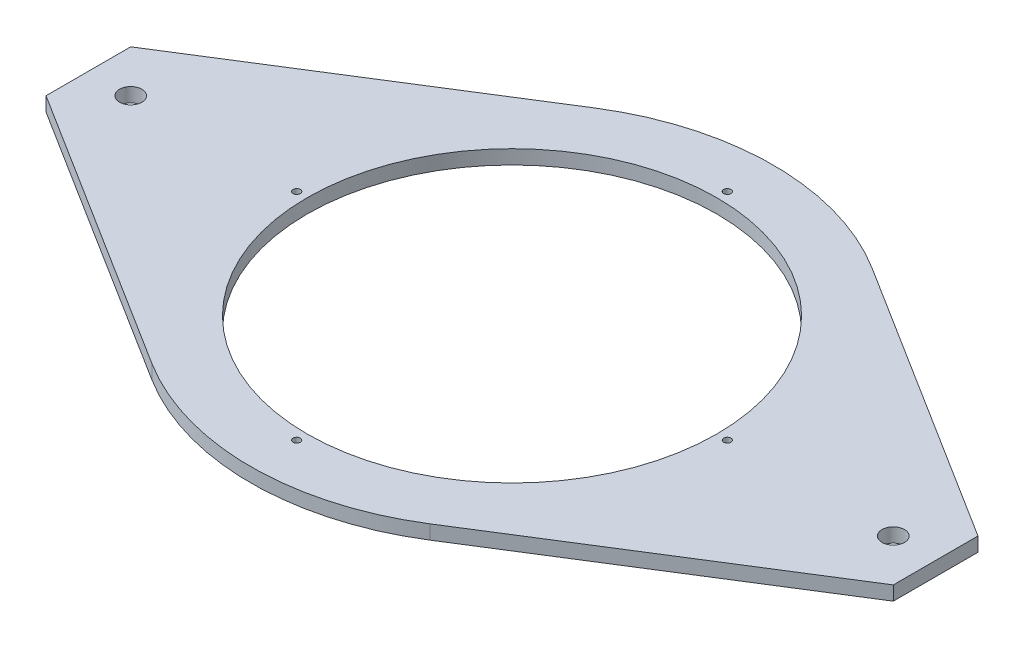
SolidWorks part; units mm, degrees
material "6061-T6 (SS)"
ref_plane "Front Plane" through (0, 0, 0) normal (0, 0, 1) x (1, 0, 0)
ref_plane "Top Plane" through (0, 0, 0) normal (0, 1, 0) x (1, 0, 0)
ref_plane "Right Plane" through (0, 0, 0) normal (1, 0, 0) x (0, 0, -1)
sketch "Sketch1" plane through (0, 0, 0) normal (0, 1, 0) x (1, 0, 0)
  line L2 (-190.5, 19.05) -> (-190.5, -19.05)
  line L4 (190.5, 19.05) -> (190.5, -19.05)
  line L5 (-190.5, 19.05) -> (190.5, -19.05) construction
  line L6 (-190.5, -19.05) -> (190.5, 19.05) construction
  line L8 (-190.5, 19.05) -> (-62.4957, 99.4719)
  line L9 (-190.5, -19.05) -> (-62.4957, -99.4719)
  line L10 (190.5, 19.05) -> (62.4957, 99.4719)
  line L11 (190.5, -19.05) -> (62.4957, -99.4719)
  circle A0 centre (0, 0) radius 92.075
  arc A1 (-62.4957, -99.4719) -> (62.4957, -99.4719) centre (0, 0) ccw
  arc A2 (62.4957, 99.4719) -> (-62.4957, 99.4719) centre (0, 0) ccw
  point P0 (0, 0)
  dimension "D3" = 184.15
  dimension "D4" = 25.4
  dimension "D1" = 381
  dimension "D2" = 38.1
extrude "Boss-Extrude1" add sketch "Sketch1" along normal blind 6.35
hole_wizard "#4 Clearance Hole1" positions "Sketch2" profile "Sketch3" hole size "#4" standard "ANSI Inch" end condition through all
sketch "Sketch2" plane through (0, 6.35, 0) normal (0, 1, 0) x (1, 0, 0)
  circle A0 centre (0, 0) radius 96.8375
  circle A1 centre (0, 0) radius 92.075 construction
  point P7 (0, 96.8375)
  point P9 (96.8375, 0)
  point P11 (0, -96.8375)
  point P13 (-96.8375, 0)
  dimension "D1" = 4.7625
sketch "Sketch3" plane through (0, 6.35, -96.8375) normal (1, 0, 0) x (0, 0, 1)
  line L0 (0, 0) -> (0, 6.35)
  line L1 (0, 6.35) -> (1.6319, 6.35)
  line L2 (1.6319, 6.35) -> (1.6319, 0)
  line L5 (1.6319, 0) -> (0, 0)
  line L11 (0, -6.35) -> (0, 107.95) construction
  dimension "Thru Hole Dia." = 3.2639
  dimension "Thru Hole Depth" = 6.35
hole_wizard "3/8 Clearance Hole1" positions "Sketch4" profile "Sketch5" hole size "3/8" standard "ANSI Inch" end condition through all
sketch "Sketch4" plane through (0, 6.35, 0) normal (0, 1, 0) x (1, 0, 0)
  line L0 (-171.45, 0) -> (171.45, 0) construction
  point P0 (-171.45, 0)
  point P2 (171.45, 0)
  dimension "D1" = 342.9
sketch "Sketch5" plane through (-171.45, 6.35, 0) normal (1, 0, 0) x (0, 0, 1)
  line L0 (0, 0) -> (0, 6.35)
  line L1 (0, 6.35) -> (5.0419, 6.35)
  line L2 (5.0419, 6.35) -> (5.0419, 0)
  line L5 (5.0419, 0) -> (0, 0)
  line L11 (0, -6.35) -> (0, 107.95) construction
  dimension "Thru Hole Dia." = 10.0838
  dimension "Thru Hole Depth" = 6.35
